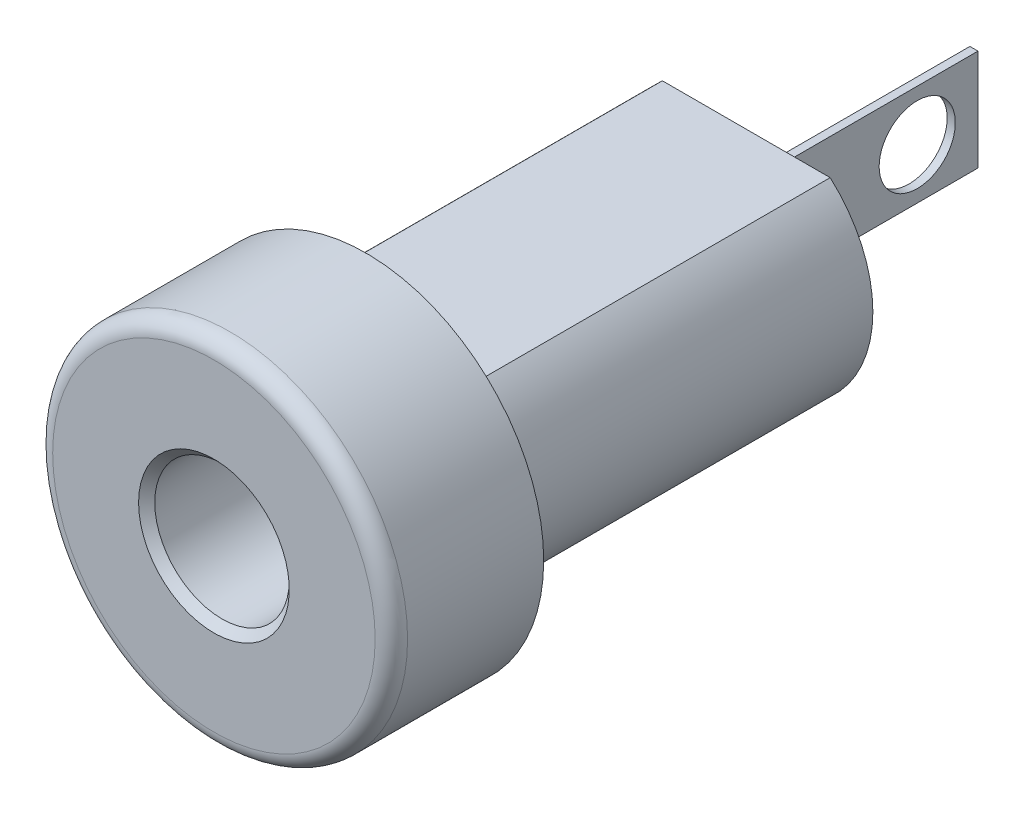
SolidWorks part; units mm, degrees
ref_plane "Front Plane" through (0, 0, 0) normal (0, 0, 1) x (1, 0, 0)
ref_plane "Top Plane" through (0, 0, 0) normal (0, 1, 0) x (1, 0, 0)
ref_plane "Right Plane" through (0, 0, 0) normal (1, 0, 0) x (0, 0, -1)
sketch "Sketch1" plane through (0, 0, 0) normal (1, 0, 0) x (0, 0, -1)
  line L0 (0, 0) -> (93.4758, 0) construction
  line L1 (0, 0) -> (0, 5.5626)
  line L2 (0, 5.5626) -> (4.7752, 5.5626)
  line L3 (4.7752, 5.5626) -> (4.7752, 3.9688)
  line L4 (4.7752, 3.9688) -> (16.6878, 3.9688)
  line L5 (16.6878, 3.9688) -> (16.6878, 0)
  line L6 (0, 0) -> (16.6878, 0)
  dimension "D1" = 4.7752
  dimension "D2" = 7.9375
  dimension "D3" = 11.9126
  dimension "D4" = 11.1252
revolve "Revolve1" add sketch "Sketch1" angle 360 about L0
fillet "Fillet1" radius 0.508 1 edges at (5.5626, 0, 0)
sketch "Sketch2" plane through (0, 0, -16.6878) normal (0, 0, -1) x (-1, 0, 0)
  line L1 (4.7022, -2.9718) -> (-4.7022, -2.9718)
  line L2 (4.7022, -2.9718) -> (4.7022, 2.9718)
  line L3 (4.7022, 2.9718) -> (-4.7022, 2.9718)
  line L4 (-4.7022, -2.9718) -> (-4.7022, 2.9718)
  line L5 (4.7022, -2.9718) -> (-4.7022, 2.9718) construction
  line L6 (4.7022, 2.9718) -> (-4.7022, -2.9718) construction
  circle A0 centre (0, 0) radius 5.5626 construction
  point P0 (0, 0)
  dimension "D1" = 5.9436
extrude "Cut-Extrude1" cut sketch "Sketch2" against normal up to surface (11.9126 mm away) flip side to cut up to face at (5.5626, 0, -4.7752)
sketch "Sketch3" plane through (0, 0, -16.6878) normal (0, 0, -1) x (-1, 0, 0)
  line L1 (0.127, -1.5875) -> (-0.127, -1.5875)
  line L2 (0.127, -1.5875) -> (0.127, 1.5875)
  line L3 (0.127, 1.5875) -> (-0.127, 1.5875)
  line L4 (-0.127, -1.5875) -> (-0.127, 1.5875)
  line L5 (0.127, -1.5875) -> (-0.127, 1.5875) construction
  line L6 (0.127, 1.5875) -> (-0.127, -1.5875) construction
  point P0 (0, 0)
  dimension "D1" = 0.254
  dimension "D2" = 3.175
extrude "Boss-Extrude1" add sketch "Sketch3" along normal blind 7.1374
sketch "Sketch4" plane through (-0.127, 0, 0) normal (-1, 0, 0) x (0, 0, 1)
  line L0 (-23.8252, 0) -> (-21.9202, 0) construction
  line L1 (-23.8252, -1.5875) -> (-23.8252, 1.5875) construction
  circle A0 centre (-21.9202, 0) radius 1.1938
  dimension "D1" = 2.3876
  dimension "D2" = 1.905
extrude "Cut-Extrude2" cut sketch "Sketch4" against normal blind 7.1374
sketch "Sketch5" plane through (-0.127, 0, 0) normal (-1, 0, 0) x (0, 0, 1)
  line L0 (-16.6878, 1.5875) -> (-16.6878, 1.2065)
  line L1 (-16.6878, -1.5875) -> (-16.6878, 1.5875) construction
  line L2 (-16.6878, 1.2065) -> (-17.3228, 1.5875)
  line L3 (-23.8252, 1.5875) -> (-16.6878, 1.5875) construction
  line L4 (-16.6878, 0) -> (-18.6168, 0) construction
  line L5 (-16.6878, 2.9718) -> (-16.6878, -2.9718) construction
  line L6 (-16.6878, -1.2065) -> (-17.3228, -1.5875)
  line L7 (-16.6878, -1.5875) -> (-16.6878, -1.2065)
  line L8 (-16.6878, 1.5875) -> (-17.3228, 1.5875)
  line L9 (-16.6878, -1.5875) -> (-17.3228, -1.5875)
  dimension "D1" = 0.635
  dimension "D2" = 0.381
extrude "Cut-Extrude3" cut sketch "Sketch5" against normal blind 7.1374
sketch "Sketch7" plane through (0, 0, 0) normal (0, 0, 1) x (1, 0, 0)
  circle A0 centre (0, 0) radius 2.1082
  dimension "D1" = 4.2164
extrude "Cut-Extrude4" cut sketch "Sketch7" against normal blind 15.875
chamfer "Chamfer2" distance 0.254 angle 45 1 edges at (2.1082, 0, 0)
sketch "recommended cutout" plane through (0, 0, -4.7752) normal (0, 0, -1) x (-1, 0, 0)
  line L0 (2.6966, 3.175) -> (-2.6966, 3.175)
  line L3 (2.6966, -3.175) -> (-2.6966, -3.175)
  arc A0 (2.6966, -3.175) -> (2.6966, 3.175) centre (0, 0) ccw
  arc A1 (-2.6966, 3.175) -> (-2.6966, -3.175) centre (0, 0) ccw
  dimension "D1" = 8.3312
  dimension "D2" = 6.35
